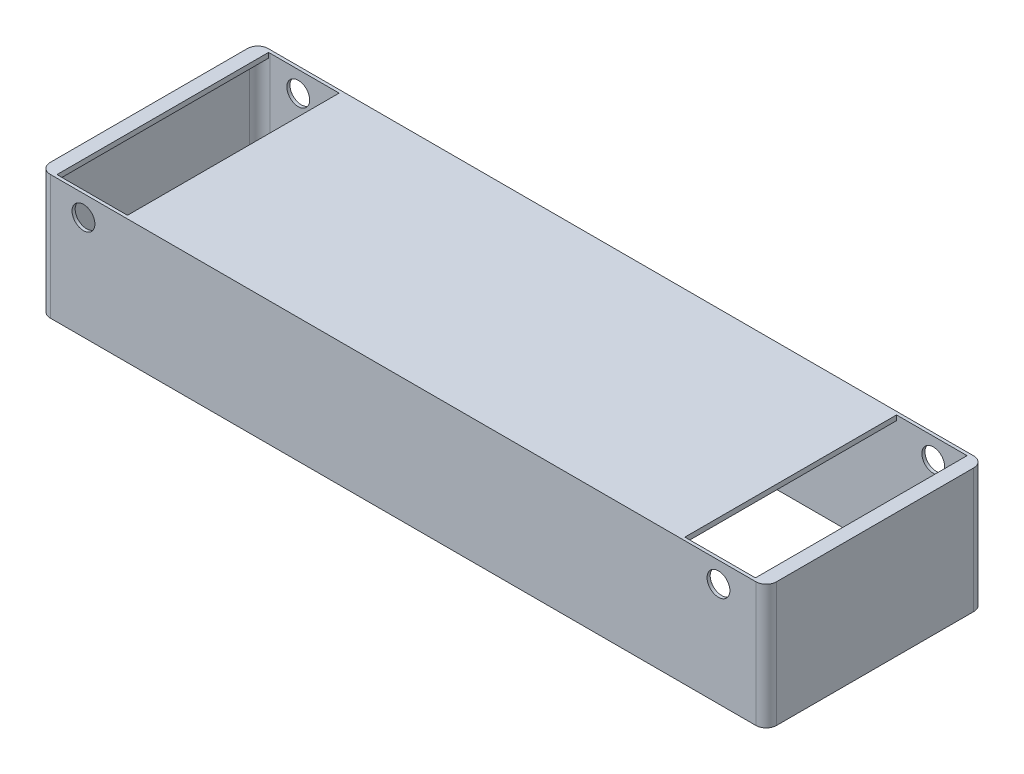
SolidWorks part; units mm, degrees
ref_plane "Alzado" through (0, 0, 0) normal (0, 0, 1) x (1, 0, 0)
ref_plane "Planta" through (0, 0, 0) normal (0, 1, 0) x (1, 0, 0)
ref_plane "Vista lateral" through (0, 0, 0) normal (1, 0, 0) x (0, 0, -1)
sketch "Croquis2" plane through (0, 0, 0) normal (0, 1, 0) x (1, 0, 0)
  line L1 (-170, 52.5) -> (170, 52.5)
  line L2 (-175, 47.5) -> (-175, -47.5)
  line L3 (-170, -52.5) -> (170, -52.5)
  line L4 (175, 47.5) -> (175, -47.5)
  line L7 (-167.6, 51) -> (167.6, 51)
  line L8 (-172.6, 46) -> (-172.6, -46)
  line L9 (-167.6, -51) -> (167.6, -51)
  line L10 (172.6, 46) -> (172.6, -46)
  arc A0 (170, -52.5) -> (175, -47.5) centre (170, -47.5) ccw
  arc A1 (167.6, -51) -> (172.6, -46) centre (167.6, -46) ccw
  arc A2 (167.6, 51) -> (172.6, 46) centre (167.6, 46) cw
  arc A3 (170, 52.5) -> (175, 47.5) centre (170, 47.5) cw
  arc A4 (-175, -47.5) -> (-170, -52.5) centre (-170, -47.5) ccw
  arc A5 (-172.6, -46) -> (-167.6, -51) centre (-167.6, -46) ccw
  arc A6 (-170, 52.5) -> (-175, 47.5) centre (-170, 47.5) ccw
  arc A7 (-167.6, 51) -> (-172.6, 46) centre (-167.6, 46) ccw
  point P0 (0, 0)
  point P5 (0, 0)
  point P15 (172.6, -51)
  point P18 (172.6, 51)
  point P21 (175, 52.5)
  point P24 (-175, -52.5)
  point P29 (-175, 52.5)
  point P32 (-172.6, 51)
  dimension "D5" = 5
  dimension "D1" = 105
  dimension "D2" = 350
  dimension "D3" = 102
  dimension "D4" = 345.2
extrude "Saliente-Extruir1" add sketch "Croquis2" along normal blind 60
sketch "Croquis3" plane through (0, 60, 0) normal (0, 1, 0) x (1, 0, 0)
  line L0 (-175, 47.5) -> (-175, 52.5) construction
  line L1 (-175, 52.5) -> (-170, 52.5) construction
  line L3 (-170, 52.5) -> (-168.3, 52.5)
  line L4 (-175, 47.5) -> (-175, -47.5)
  line L5 (-170, -52.5) -> (-168.3, -52.5)
  line L6 (-168.3, 52.5) -> (-168.3, -52.5)
  line L7 (-170, -52.5) -> (170, -52.5) construction
  line L8 (167.6, 51) -> (-167.6, 51) construction
  line L9 (0, 0) -> (0, 51) construction
  line L10 (170, 52.5) -> (168.3, 52.5)
  line L11 (170, -52.5) -> (168.3, -52.5)
  line L12 (168.3, 52.5) -> (168.3, -52.5)
  line L13 (175, 47.5) -> (175, -47.5)
  line L14 (-134.3, 52.5) -> (134.3, 52.5)
  line L15 (-134.3, 52.5) -> (-134.3, -52.5)
  line L16 (-134.3, -52.5) -> (134.3, -52.5)
  line L17 (134.3, 52.5) -> (134.3, -52.5)
  line L18 (-134.3, 52.5) -> (134.3, -52.5) construction
  line L19 (-134.3, -52.5) -> (134.3, 52.5) construction
  arc A0 (-170, 52.5) -> (-175, 47.5) centre (-170, 47.5) ccw
  arc A1 (-175, -47.5) -> (-170, -52.5) centre (-170, -47.5) ccw
  arc A2 (170, 52.5) -> (175, 47.5) centre (170, 47.5) cw
  arc A3 (175, -47.5) -> (170, -52.5) centre (170, -47.5) cw
  point P15 (-175, -52.5)
  dimension "D3" = 5
  dimension "D1" = 105
  dimension "D2" = 6.7
  dimension "D4" = 34
extrude "Saliente-Extruir4" add sketch "Croquis3" against normal blind 2.4
sketch "Croquis4" plane through (0, 0, 52.5) normal (0, 0, 1) x (1, 0, 0)
  line L0 (-170, 50) -> (-154, 50) construction
  line L1 (-170, 60) -> (-170, 0) construction
  line L2 (-154, 50) -> (152, 50) construction
  line L3 (152, 50) -> (170, 50) construction
  line L4 (170, 60) -> (170, 0) construction
  line L6 (-170, 60) -> (170, 60) construction
  circle A0 centre (152, 50) radius 5.5
  circle A1 centre (-154, 50) radius 5.5
  dimension "D4" = 11
  dimension "D1" = 16
  dimension "D2" = 306
  dimension "D3" = 10
extrude "Cortar-Extruir1" cut sketch "Croquis4" against normal through all
